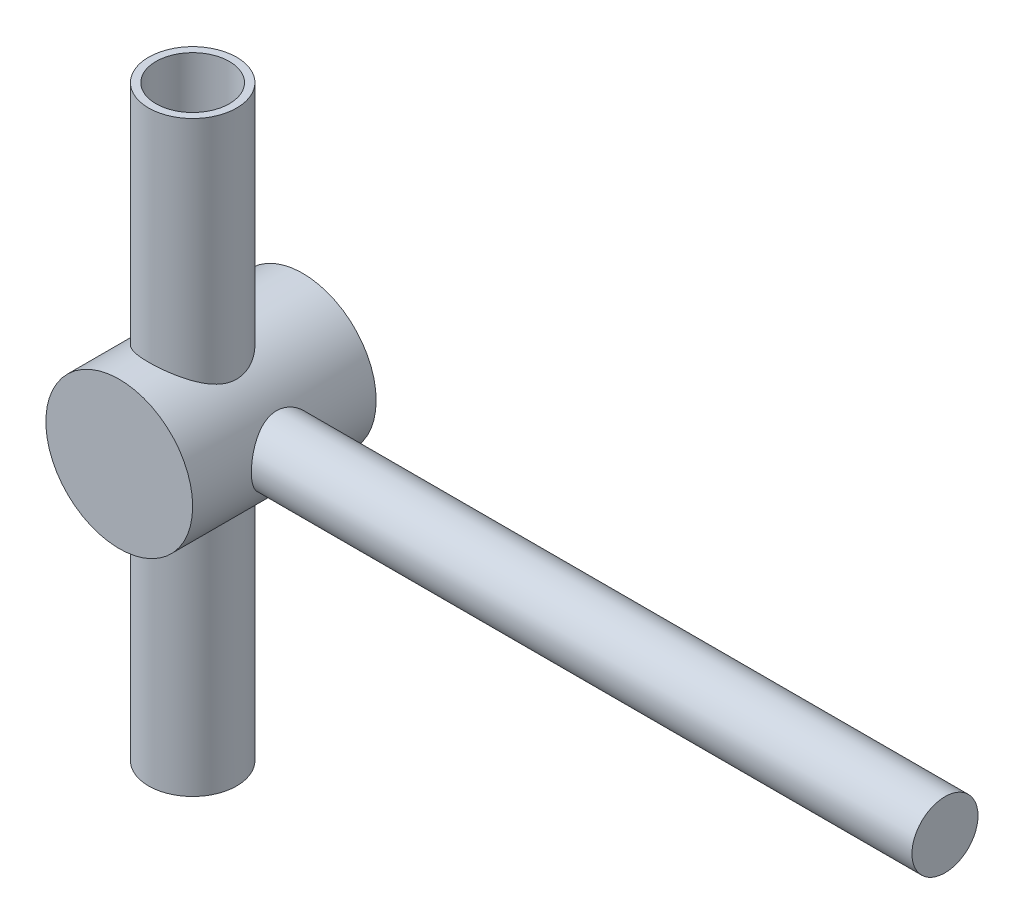
SolidWorks part; units mm, degrees
ref_plane "Front Plane" through (0, 0, 0) normal (0, 0, 1) x (1, 0, 0)
ref_plane "Top Plane" through (0, 0, 0) normal (0, 1, 0) x (1, 0, 0)
ref_plane "Right Plane" through (0, 0, 0) normal (1, 0, 0) x (0, 0, -1)
sketch "Sketch1" plane through (0, 0, 0) normal (0, 0, 1) x (1, 0, 0)
  circle A0 centre (0, 0) radius 5
  dimension "D1" = 10
extrude "Boss-Extrude1" add sketch "Sketch1" along normal mid plane 12.5
sketch "Sketch2" plane through (0, 0, 0) normal (0, 1, 0) x (1, 0, 0)
  line L3 (-5, -6.25) -> (5, -6.25) construction
  line L4 (5, -6.25) -> (5, 6.25) construction
  circle A0 centre (0, -1.25) radius 3
  dimension "D1" = 6
  dimension "D3" = 5
  dimension "D2" = 5
extrude "Boss-Extrude2" add sketch "Sketch2" along normal mid plane 40
sketch "Sketch3" plane through (0, 0, 0) normal (1, 0, 0) x (0, 0, -1)
  circle A0 centre (0, 0) radius 2.25
  dimension "D1" = 4.5
extrude "Boss-Extrude3" add sketch "Sketch3" along normal blind 50
sketch "Sketch4" plane through (0, -20, 0) normal (0, -1, 0) x (1, 0, 0)
  circle A0 centre (0, 1.25) radius 2.5
  circle A1 centre (0, 1.25) radius 3 construction
  dimension "D1" = 5
extrude "Cut-Extrude1" cut sketch "Sketch4" against normal up to next (40 mm away) from surface at 0 starting at face at (0, -20, 4.25)
sketch "Sketch5" plane through (0, 0, 6.25) normal (0, 0, 1) x (1, 0, 0)
  circle A0 centre (0, 0) radius 3.75
  dimension "D1" = 7.5
extrude "Cut-Extrude2" cut sketch "Sketch5" along normal blind 10 from surface at -12.5 starting at face at (5, 0, -6.25)
